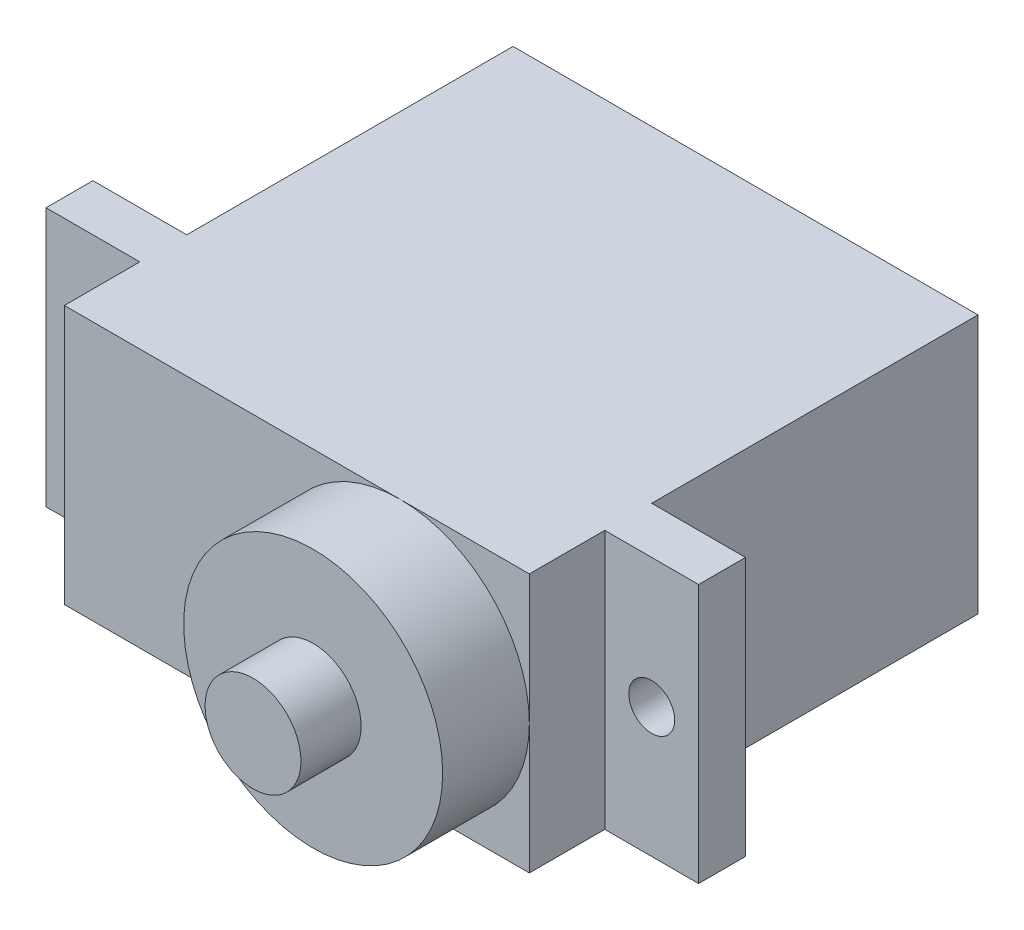
SolidWorks part; units mm, degrees
ref_plane "Front" through (0, 0, 0) normal (0, 0, 1) x (1, 0, 0)
ref_plane "Top" through (0, 0, 0) normal (0, 1, 0) x (1, 0, 0)
ref_plane "Right" through (0, 0, 0) normal (1, 0, 0) x (0, 0, -1)
sketch "Sketch1" plane through (0, 0, 0) normal (0, 0, 1) x (1, 0, 0)
  line L1 (-11.4, -6.35) -> (11.4, -6.35)
  line L2 (-11.4, -6.35) -> (-11.4, 6.35)
  line L3 (-11.4, 6.35) -> (11.4, 6.35)
  line L4 (11.4, -6.35) -> (11.4, 6.35)
  line L5 (-11.4, -6.35) -> (11.4, 6.35) construction
  line L6 (-11.4, 6.35) -> (11.4, -6.35) construction
  point P0 (0, 0)
  dimension "D1" = 22.8
  dimension "D2" = 12.7
extrude "Body" add sketch "Sketch1" along normal blind 22 contours L3 L4 L1 L2
ref_plane "ConnectorPlane" through (0, 0, 16) normal (0, 0, -1) x (-1, 0, 0)
sketch "Sketch2" plane through (0, 0, 16) normal (0, 0, -1) x (-1, 0, 0)
  line L0 (11.4, -6.35) -> (11.4, 6.35) construction
  line L1 (-11.4, -6.35) -> (-11.4, 6.35) construction
  line L2 (11.4, -6.35) -> (11.4, 6.35)
  line L3 (-11.4, -6.35) -> (-11.4, 6.35)
  line L4 (11.4, 6.35) -> (16, 6.35)
  line L5 (16, 6.35) -> (16, -6.35)
  line L6 (16, -6.35) -> (11.4, -6.35)
  line L7 (-11.4, 6.35) -> (-16, 6.35)
  line L8 (-16, 6.35) -> (-16, -6.35)
  line L9 (-16, -6.35) -> (-11.4, -6.35)
  line L10 (-16, 0) -> (-11.4, 0) construction
  line L11 (16, 0) -> (11.4, 0) construction
  circle A0 centre (-13.7, 0) radius 1.125
  circle A1 centre (13.7, 0) radius 1.125
  dimension "D2" = 2.25
  dimension "D1" = 32
extrude "Boss-Extrude2" add sketch "Sketch2" against normal blind 2.3 contours L8 L9 L3 L7 | L6 L5 L4 L2 A1
sketch "Sketch3" plane through (0, 0, 22) normal (0, 0, 1) x (1, 0, 0)
  line L0 (5.05, 6.35) -> (5.05, -6.35) construction
  line L1 (-11.4, 6.35) -> (11.4, 6.35) construction
  line L2 (-11.4, -6.35) -> (11.4, -6.35) construction
  line L4 (11.4, -6.35) -> (11.4, 6.35) construction
  circle A0 centre (5.05, 0) radius 2.35
  arc A1 (5.05, 6.35) -> (5.05, -6.35) centre (5.05, 0) cw
  dimension "D1" = 4.7
extrude "Boss-Extrude3" add sketch "Sketch3" along normal offset from surface (7.2 mm away) 29.2 contours A0 up to face at (0, 0, 0)
sketch "Sketch4" plane through (0, 0, 22) normal (0, 0, 1) x (1, 0, 0)
  line L0 (11.4, -6.35) -> (11.4, 6.35) construction
  circle A0 centre (5.05, 0) radius 6.35
extrude "Boss-Extrude4" add sketch "Sketch4" along normal blind 4.25 contours A0
